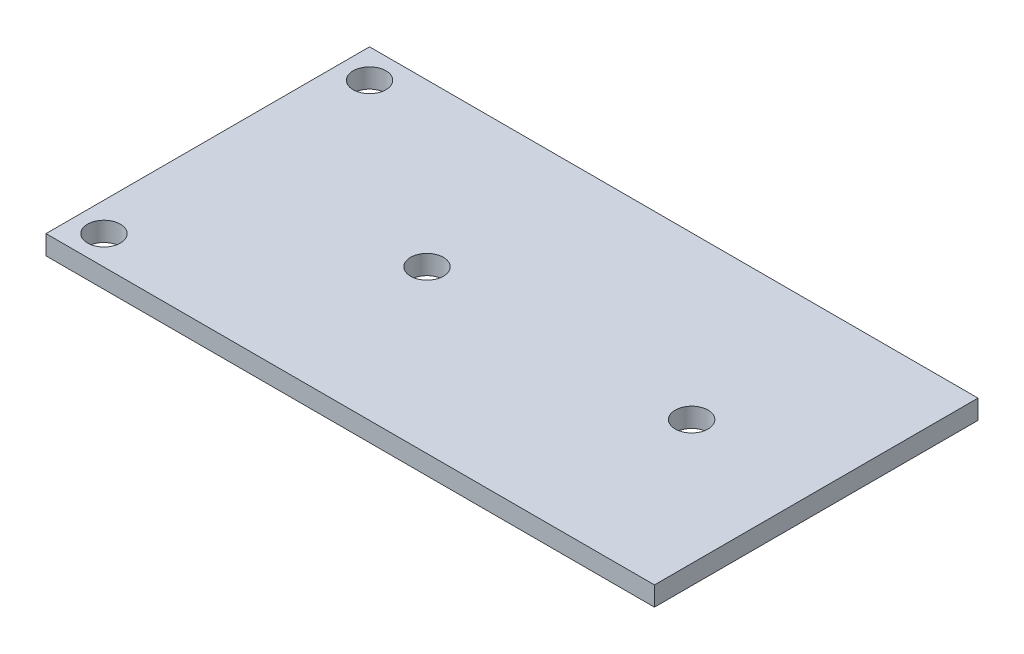
SolidWorks part; units mm, degrees
ref_plane "Front Plane" through (0, 0, 0) normal (0, 0, 1) x (1, 0, 0)
ref_plane "Top Plane" through (0, 0, 0) normal (0, 1, 0) x (1, 0, 0)
ref_plane "Right Plane" through (0, 0, 0) normal (1, 0, 0) x (0, 0, -1)
sketch "Sketch1" plane through (0, 0, 0) normal (0, 1, 0) x (1, 0, 0)
  line L1 (-72.1861, 30.4945) -> (-7.1861, 30.4945)
  line L2 (-72.1861, 30.4945) -> (-72.1861, -3.0055)
  line L3 (-72.1861, -3.0055) -> (-7.1861, -3.0055)
  line L4 (-7.1861, 30.4945) -> (-7.1861, -3.0055)
  dimension "D1" = 65
  dimension "D2" = 33.5
extrude "Boss-Extrude1" add sketch "Sketch1" along normal blind 2
hole_wizard "M3 Clearance Hole1" positions "Sketch3" profile "Sketch2" hole size "M3" standard "ANSI Metric" end condition through all
sketch "Sketch3" plane through (0, 2, 0) normal (0, 1, 0) x (1, 0, 0)
  line L0 (-7.1861, 30.4945) -> (-72.1861, 30.4945) construction
  line L1 (-72.1861, -3.0055) -> (-7.1861, -3.0055) construction
  line L2 (-72.1861, 30.4945) -> (-72.1861, -3.0055) construction
  point P0 (-67.1861, 27.4945)
  point P2 (-67.1861, -0.0055)
  dimension "D1" = 3
  dimension "D2" = 3
  dimension "D3" = 5
  dimension "D4" = 5
sketch "Sketch2" plane through (-67.1861, 2, -27.4945) normal (1, 0, 0) x (0, 0, 1)
  line L0 (0, 0) -> (0, 2)
  line L1 (0, 2) -> (1.7, 2)
  line L2 (1.7, 2) -> (1.7, 0)
  line L5 (1.7, 0) -> (0, 0)
  line L11 (0, -6.35) -> (0, 107.95) construction
  dimension "Thru Hole Dia." = 3.4
  dimension "Thru Hole Depth" = 2
hole_wizard "M3 Clearance Hole2" positions "3DSketch1" profile "Sketch5" hole size "M3" standard "ANSI Metric" end condition through all
sketch3d "3DSketch1"
  line L0 (-72.1861, 2, -30.4945) -> (-72.1861, 2, 3.0055) construction
  line L1 (-72.1861, 2, 3.0055) -> (-7.1861, 2, 3.0055) construction
  point P0 (-47.4861, 2, -13.7445)
  point P2 (-20.0861, 2, -13.7445)
  dimension "D1" = 24.7
  dimension "D2" = 27.4
  dimension "D3" = 16.75
  dimension "D4" = 16.75
sketch "Sketch5" plane through (-47.4861, 2, -13.7445) normal (1, 0, 0) x (0, 0, 1)
  line L0 (0, 0) -> (0, 2)
  line L1 (0, 2) -> (1.7, 2)
  line L2 (1.7, 2) -> (1.7, 0)
  line L5 (1.7, 0) -> (0, 0)
  line L11 (0, -6.35) -> (0, 107.95) construction
  dimension "Thru Hole Dia." = 3.4
  dimension "Thru Hole Depth" = 2
sketch "Sketch6" plane through (0, 0, 0) normal (0, -1, 0) x (1, 0, 0)
  line L0 (-72.1861, 3.0055) -> (-7.1861, 3.0055) construction
  line L1 (-72.1861, -30.4945) -> (-70.1861, -30.4945)
  line L2 (-72.1861, -30.4945) -> (-72.1861, 3.0055)
  line L3 (-72.1861, 3.0055) -> (-70.1861, 3.0055)
  line L4 (-70.1861, -30.4945) -> (-70.1861, 3.0055)
  dimension "D1" = 2
extrude "Cut-Extrude1" cut sketch "Sketch6" against normal through all
